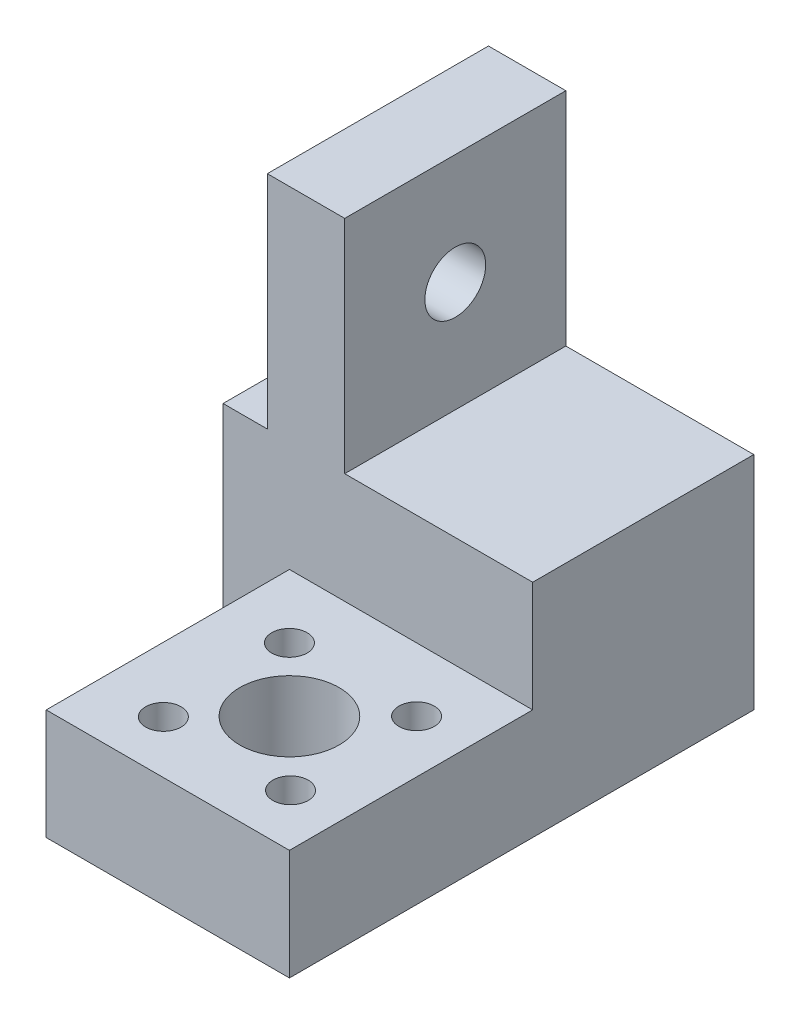
SolidWorks part; units mm, degrees
ref_plane "Front Plane" through (0, 0, 0) normal (0, 0, 1) x (1, 0, 0)
ref_plane "Top Plane" through (0, 0, 0) normal (0, 1, 0) x (1, 0, 0)
ref_plane "Right Plane" through (0, 0, 0) normal (1, 0, 0) x (0, 0, -1)
sketch "Sketch1" plane through (0, 0, 0) normal (0, 1, 0) x (1, 0, 0)
  line L1 (-11, 11) -> (11, 11)
  line L2 (-11, 11) -> (-11, -11)
  line L3 (-11, -11) -> (11, -11)
  line L4 (11, 11) -> (11, -11)
  circle A0 centre (0, 0) radius 11 construction
  circle A1 centre (-5.25, 5.25) radius 1.6
  circle A2 centre (6.25, 5.25) radius 1.6
  circle A3 centre (6.3486, -6.25) radius 1.6
  circle A5 centre (-5.1514, -6.25) radius 1.6
  dimension "D1" = 22
  dimension "D2" = 3.2
  dimension "D3" = 11.5
  dimension "D4" = 11.5
  dimension "D5" = 11.5
  dimension "D6" = 11.5
  dimension "D7" = 5.25
  dimension "D8" = 5.25
extrude "Boss-Extrude1" add sketch "Sketch1" along normal blind 10
sketch "Sketch2" plane through (0, 0, -11) normal (0, 0, -1) x (-1, 0, 0)
  line L1 (-11, 0) -> (17, 0)
  line L2 (-11, 0) -> (-11, 20)
  line L3 (-11, 20) -> (17, 20)
  line L4 (17, 0) -> (17, 20)
  dimension "D1" = 20
  dimension "D2" = 28
extrude "Boss-Extrude2" add sketch "Sketch2" along normal blind 20
sketch "Sketch3" plane through (0, 20, 0) normal (0, 1, 0) x (1, 0, 0)
  line L0 (-17, 11) -> (11, 11) construction
  line L1 (-13, 11) -> (-6, 11)
  line L2 (-13, 11) -> (-13, 31)
  line L3 (-13, 31) -> (-6, 31)
  line L4 (-6, 11) -> (-6, 31)
  line L5 (11, 31) -> (11, 11) construction
  dimension "D1" = 20
  dimension "D2" = 7
  dimension "D3" = 17
extrude "Boss-Extrude3" add sketch "Sketch3" along normal blind 20
sketch "Sketch4" plane through (-6, 0, 0) normal (1, 0, 0) x (0, 0, -1)
  line L0 (11, 20) -> (31, 20) construction
  line L1 (31, 40) -> (31, 20) construction
  circle A0 centre (21, 30) radius 2.75
  point P6 (31, 30)
  dimension "D1" = 5.5
  dimension "D3" = 10
  dimension "D2" = 10
extrude "Cut-Extrude1" cut sketch "Sketch4" against normal through all
sketch "Sketch5" plane through (0, 10, 0) normal (0, 1, 0) x (1, 0, 0)
  circle A0 centre (0.5, -0.5) radius 4.5
  circle A2 centre (-5.25, 5.25) radius 1.6 construction
  point P3 (0, 0)
  dimension "D1" = 9
  dimension "D2" = 5.75
  dimension "D3" = 5.75
extrude "Cut-Extrude2" cut sketch "Sketch5" against normal through all
